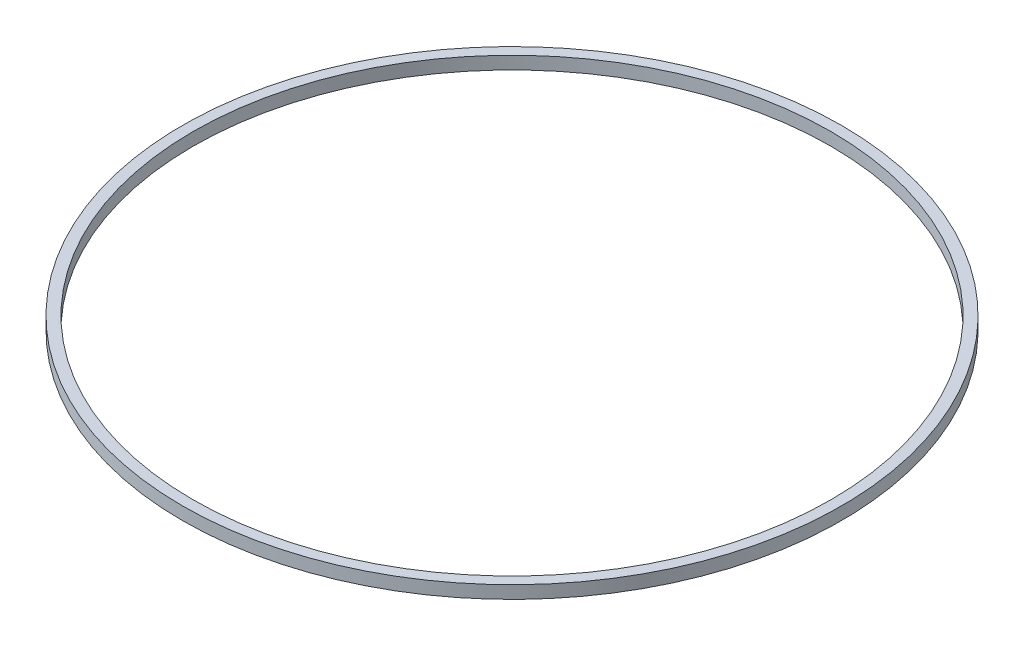
SolidWorks part; units mm, degrees
ref_plane "Front Plane" through (0, 0, 0) normal (0, 0, 1) x (1, 0, 0)
ref_plane "Top Plane" through (0, 0, 0) normal (0, 1, 0) x (1, 0, 0)
ref_plane "Right Plane" through (0, 0, 0) normal (1, 0, 0) x (0, 0, -1)
sketch "Sketch1" plane through (0, 0, 0) normal (0, 1, 0) x (1, 0, 0)
  circle A2 centre (0, 0) radius 77.5
  circle A3 centre (0, 0) radius 75
  dimension "D1" = 155
  dimension "D2" = 150
extrude "Boss-Extrude1" add sketch "Sketch1" along normal blind 3
